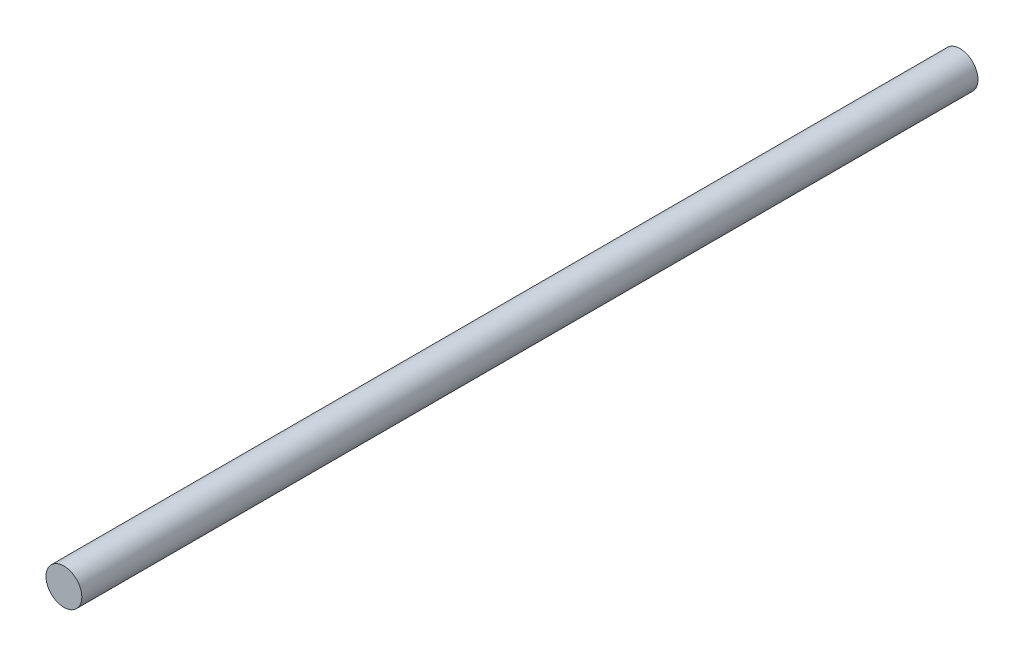
SolidWorks part; units mm, degrees
ref_plane "Front Plane" through (0, 0, 0) normal (0, 0, 1) x (1, 0, 0)
ref_plane "Top Plane" through (0, 0, 0) normal (0, 1, 0) x (1, 0, 0)
ref_plane "Right Plane" through (0, 0, 0) normal (1, 0, 0) x (0, 0, -1)
sketch "Sketch1" plane through (0, 0, 0) normal (0, 0, 1) x (1, 0, 0)
  circle A0 centre (0, 0) radius 10
extrude "Boss-Extrude1" add sketch "Sketch1" along normal blind 500
